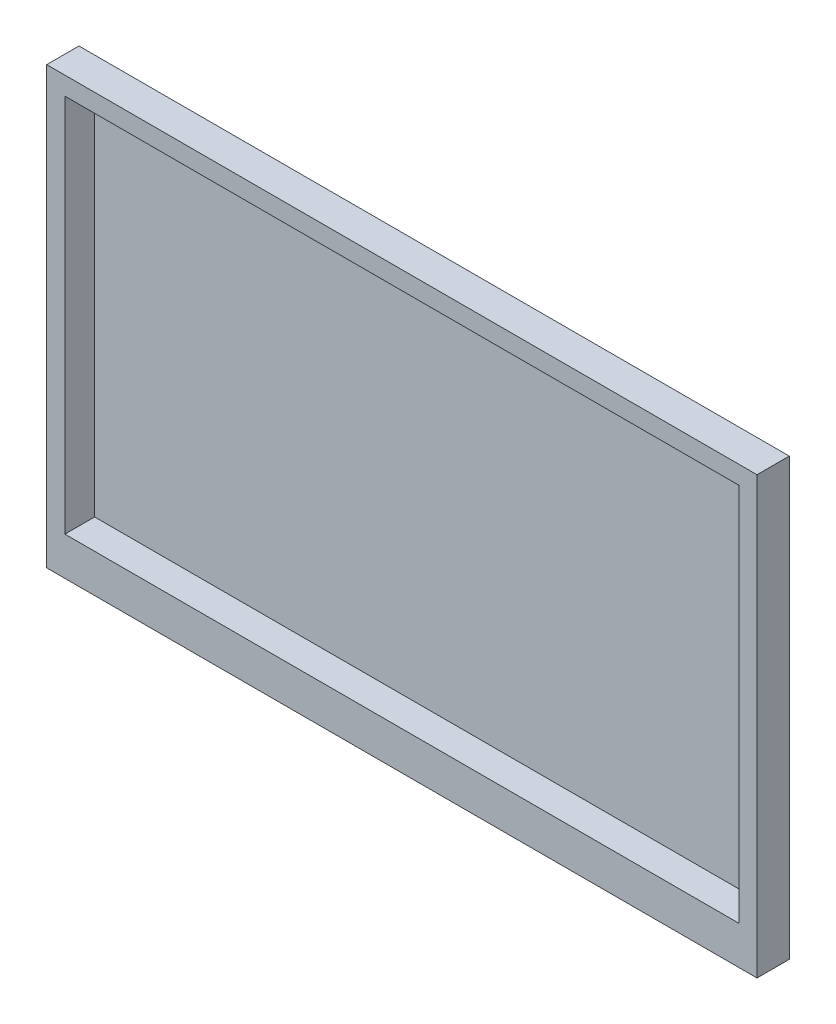
SolidWorks part; units mm, degrees
ref_plane "Front Plane" through (0, 0, 0) normal (0, 0, 1) x (1, 0, 0)
ref_plane "Top Plane" through (0, 0, 0) normal (0, 1, 0) x (1, 0, 0)
ref_plane "Right Plane" through (0, 0, 0) normal (1, 0, 0) x (0, 0, -1)
sketch "Sketch1" plane through (0, 0, 0) normal (0, 0, 1) x (1, 0, 0)
  line L0 (-265.1125, 7.9375) -> (265.1125, 7.9375) construction
  line L1 (-279.4, -171.45) -> (279.4, -171.45)
  line L2 (-279.4, -171.45) -> (-279.4, 171.45)
  line L3 (-279.4, 171.45) -> (279.4, 171.45)
  line L4 (279.4, -171.45) -> (279.4, 171.45)
  line L5 (-279.4, -171.45) -> (279.4, 171.45) construction
  line L6 (-279.4, 171.45) -> (279.4, -171.45) construction
  line L7 (-265.1125, -141.2875) -> (265.1125, -141.2875)
  line L8 (-265.1125, -141.2875) -> (-265.1125, 157.1625)
  line L9 (-265.1125, 157.1625) -> (265.1125, 157.1625)
  line L10 (265.1125, -141.2875) -> (265.1125, 157.1625)
  line L11 (0, 0) -> (0, 7.9375) construction
  line L12 (-265.1125, 7.9375) -> (-279.4, 7.9375) construction
  line L13 (0, 157.1625) -> (0, 171.45) construction
  point P0 (0, 0)
  point P6 (0, 0)
  point P11 (0, 7.9375)
  dimension "D1" = 558.8
  dimension "D2" = 342.9
  dimension "D3" = 530.225
  dimension "D4" = 298.45
extrude "Boss-Extrude1" add sketch "Sketch1" against normal blind 25.4
sketch "Sketch2" plane through (0, 0, -25.4) normal (0, 0, -1) x (-1, 0, 0)
  line L0 (265.1125, -141.2875) -> (-265.1125, -141.2875) construction
  line L1 (265.1125, 157.1625) -> (265.1125, -141.2875) construction
  line L2 (-265.1125, 157.1625) -> (265.1125, 157.1625) construction
  line L3 (-265.1125, -141.2875) -> (-265.1125, 157.1625) construction
  line L4 (265.1125, -141.2875) -> (-265.1125, -141.2875)
  line L5 (265.1125, 157.1625) -> (265.1125, -141.2875)
  line L6 (-265.1125, 157.1625) -> (265.1125, 157.1625)
  line L7 (-265.1125, -141.2875) -> (-265.1125, 157.1625)
extrude "Boss-Extrude2" add sketch "Sketch2" against normal blind 2
sketch "Sketch3" plane through (0, 0, -25.4) normal (0, 0, -1) x (-1, 0, 0)
  line L1 (-50, -50) -> (50, -50)
  line L2 (-50, -50) -> (-50, 50)
  line L3 (-50, 50) -> (50, 50)
  line L4 (50, -50) -> (50, 50)
  line L5 (-50, -50) -> (50, 50) construction
  line L6 (-50, 50) -> (50, -50) construction
  point P0 (0, 0)
  dimension "D1" = 100
extrude "Boss-Extrude3" add sketch "Sketch3" along normal blind 76.2
